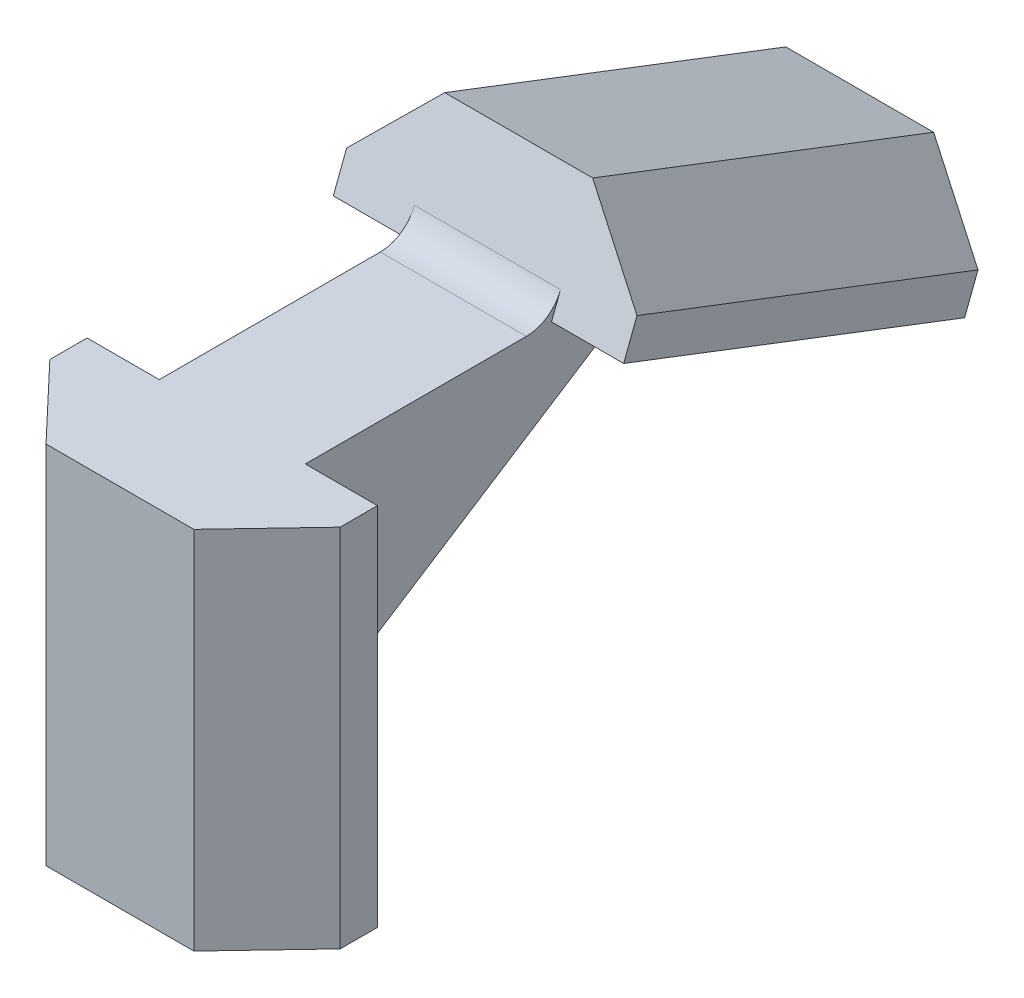
SolidWorks part; units mm, degrees
ref_plane "Front Plane" through (0, 0, 0) normal (0, 0, 1) x (1, 0, 0)
ref_plane "Top Plane" through (0, 0, 0) normal (0, 1, 0) x (1, 0, 0)
ref_plane "Right Plane" through (0, 0, 0) normal (1, 0, 0) x (0, 0, -1)
sketch "Sketch1" plane through (0, 0, 0) normal (0, 1, 0) x (1, 0, 0)
  line L4 (0, 0) -> (0, 4.5954) construction
  line B0 (7.95, 0) -> (7.95, -2.04)
  line B1 (4.048, -6.1524) -> (-4.048, -6.1524)
  line B2 (-7.95, -2.04) -> (-7.95, 0)
  line B3 (-7.95, 0) -> (7.95, 0)
  line B4 (7.95, -2.04) -> (4.048, -6.1524)
  line B5 (-4.048, -6.1524) -> (-7.95, -2.04)
  line B6 (4.05, 0) -> (-4.05, 0) construction
sketch_block_instance "Extrusion Profile-2"
sketch_block "Extrusion Profile" parameters "D1"=8.44, "D2"=2.6, "D3"=6, "D4"=16.7, "D6"=5.6686, "D7"=2.0404, "D8"=8.0963, "D9"=15.9, "D5"=2.4157
extrude "Boss-Extrude1" add sketch "Sketch1" against normal blind 20 contours B2 B5 B1 B4 B0 B3
ref_plane "Plane1" through (0, 0, 0) normal (1, 0, 0) x (0, 0, -1)
sketch "Sketch2" plane through (0, 0, 0) normal (1, 0, 0) x (0, 0, -1)
  line L10 (5.1098, 0) -> (23.7814, -7.1674)
  line L12 (5.1098, 0) -> (6.1849, 2.8007)
  line L13 (6.1849, 2.8007) -> (24.8565, -4.3666)
  line L14 (24.8565, -4.3666) -> (23.7814, -7.1674)
  line L15 (0, -20) -> (0, 0) construction
  dimension "D1" = 69
  dimension "D2" = 3
  dimension "D3" = 20
  dimension "D4" = 5.1098
sketch "Sketch4" plane through (0, 0, 0) normal (1, 0, 0) x (0, 0, -1)
  line L0 (0, 0) -> (13.4811, 0)
  line L1 (6.1849, 2.8007) -> (24.8565, -4.3666) construction
  line L2 (13.4811, 0) -> (17.2781, -1.4575)
  line L3 (17.2781, -1.4575) -> (0, -12.5397)
  line L6 (0, 0) -> (0, -12.5397)
  dimension "D1" = 10.5551
  dimension "D2" = 20.5267
extrude "Boss-Extrude3" add sketch "Sketch4" along normal mid plane 8 contours L0 L2 L3
sketch "Sketch11" plane through (0, 4.5103, -1.7313) normal (0, 0.9336, -0.3584) x (1, 0, 0)
  line L0 (-4, 16.6528) -> (-4, 12.5857)
  line L1 (-4, 12.5857) -> (4, 12.5857)
  line L2 (4, 12.5857) -> (4, 16.6528)
  line L3 (4, 16.6528) -> (-4, 16.6528)
extrude "Boss-Extrude8" add sketch "Sketch11" along normal blind 1
sketch "Sketch10" plane through (0, -4.5103, -11.7497) normal (0, 0.3584, 0.9336) x (1, 0, 0)
  line B0 (-7.95, 4.8312) -> (-7.95, 6.8712)
  line B1 (-4.048, 10.9836) -> (4.048, 10.9836)
  line B2 (7.95, 6.8712) -> (7.95, 4.8312)
  line B3 (7.95, 4.8312) -> (-7.95, 4.8312)
  line B4 (-7.95, 6.8712) -> (-4.048, 10.9836)
  line B5 (4.048, 10.9836) -> (7.95, 6.8712)
sketch_block_instance "Extrusion Profile-4"
extrude "Boss-Extrude7" add sketch "Sketch10" against normal blind 20
fillet "Fillet1" radius 2 3 edges at (0, -1.4575, -17.2781) (0, 0, -13.4811) (0, -12.5397, 0)
